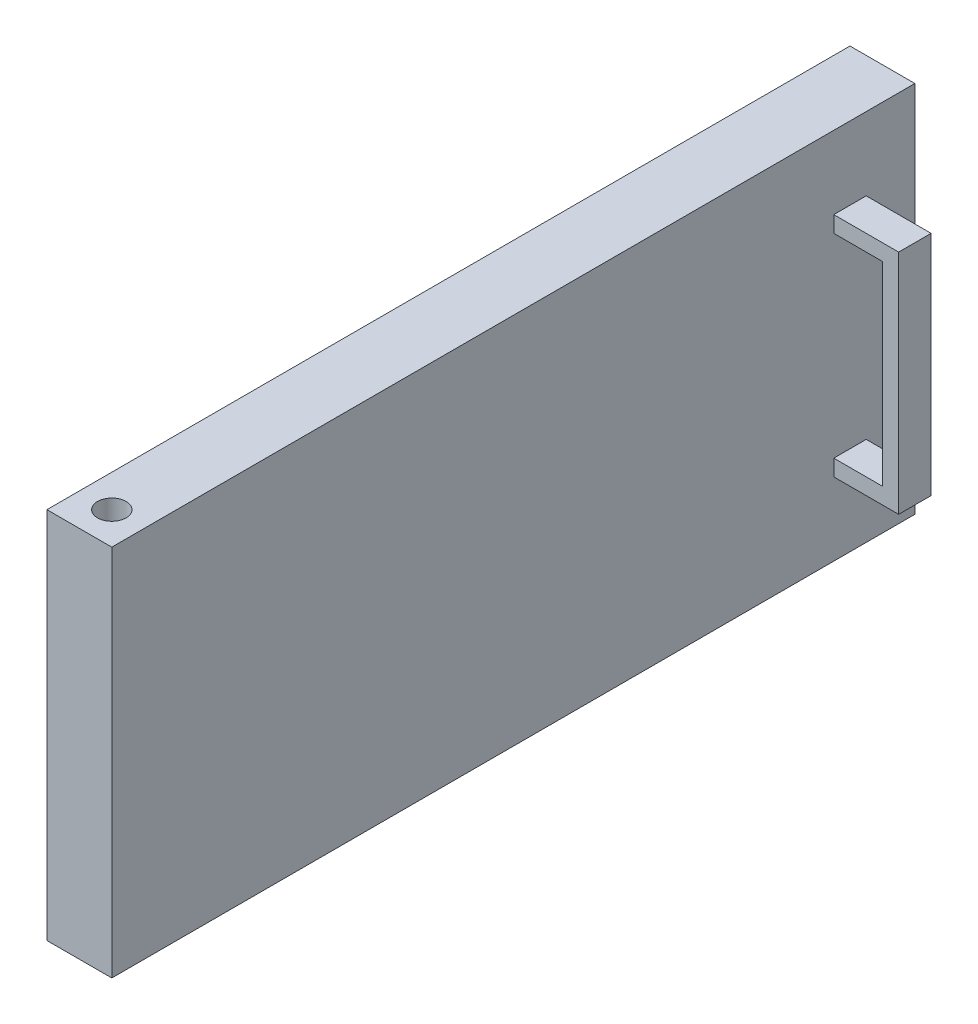
SolidWorks part; units mm, degrees
ref_plane "Front Plane" through (0, 0, 0) normal (0, 0, 1) x (1, 0, 0)
ref_plane "Top Plane" through (0, 0, 0) normal (0, 1, 0) x (1, 0, 0)
ref_plane "Right Plane" through (0, 0, 0) normal (1, 0, 0) x (0, 0, -1)
sketch "Sketch1" plane through (0, 0, 0) normal (1, 0, 0) x (0, 0, -1)
  line L1 (-123.75, 57.5) -> (123.75, 57.5)
  line L2 (-123.75, 57.5) -> (-123.75, -57.5)
  line L3 (-123.75, -57.5) -> (123.75, -57.5)
  line L4 (123.75, 57.5) -> (123.75, -57.5)
  line L5 (-123.75, 57.5) -> (123.75, -57.5) construction
  line L6 (-123.75, -57.5) -> (123.75, 57.5) construction
  point P0 (0, 0)
  dimension "D1" = 115
  dimension "D2" = 247.5
extrude "Boss-Extrude1" add sketch "Sketch1" along normal blind 20
sketch "Sketch2" plane through (0, 57.5, 0) normal (0, 1, 0) x (1, 0, 0)
  line L0 (20, -123.75) -> (0, -123.75) construction
  line L1 (20, -113.75) -> (0, -113.75) construction
  line L2 (20, 123.75) -> (20, -123.75) construction
  line L3 (0, 123.75) -> (0, -123.75) construction
  circle A0 centre (10, -113.75) radius 4.4
  dimension "D1" = 8.8
  dimension "D2" = 10
  dimension "D3" = 10
extrude "Cut-Extrude1" cut sketch "Sketch2" against normal blind 17.5
sketch "Sketch3" plane through (0, -57.5, 0) normal (0, -1, 0) x (1, 0, 0)
  line L0 (20, 123.75) -> (0, 123.75) construction
  line L1 (0, 113.75) -> (20, 113.75) construction
  line L2 (0, 123.75) -> (0, -123.75) construction
  line L3 (20, 123.75) -> (20, -123.75) construction
  circle A0 centre (10, 113.75) radius 4.4
  point P10 (10, 113.75)
  dimension "D1" = 8.8
  dimension "D2" = 10
extrude "Cut-Extrude2" cut sketch "Sketch3" against normal blind 17.5
sketch "Sketch6" plane through (20, 0, 0) normal (1, 0, 0) x (0, 0, -1)
  line L0 (123.75, -57.5) -> (123.75, 57.5) construction
  line L1 (98.75, 35) -> (108.75, 35)
  line L2 (98.75, 35) -> (98.75, -35)
  line L3 (98.75, -35) -> (108.75, -35)
  line L4 (108.75, 35) -> (108.75, -35)
  point P4 (103.75, 35)
  point P7 (123.75, 0)
  point P8 (108.75, 0)
  dimension "D1" = 70
  dimension "D2" = 10
  dimension "D3" = 20
extrude "Boss-Extrude3" add sketch "Sketch6" along normal blind 20
sketch "Sketch7" plane through (0, 0, -108.75) normal (0, 0, -1) x (-1, 0, 0)
  line L0 (-20, -57.5) -> (-20, 57.5) construction
  line L1 (-20, 30) -> (-35, 30)
  line L2 (-20, 30) -> (-20, -30)
  line L3 (-20, -30) -> (-35, -30)
  line L4 (-35, 30) -> (-35, -30)
  line L5 (-40, 35) -> (-20, 35) construction
  line L6 (-40, -35) -> (-40, 35) construction
  line L7 (-40, -35) -> (-20, -35) construction
  dimension "D1" = 5
  dimension "D2" = 5
  dimension "D3" = 5
extrude "Cut-Extrude4" cut sketch "Sketch7" against normal blind 20
